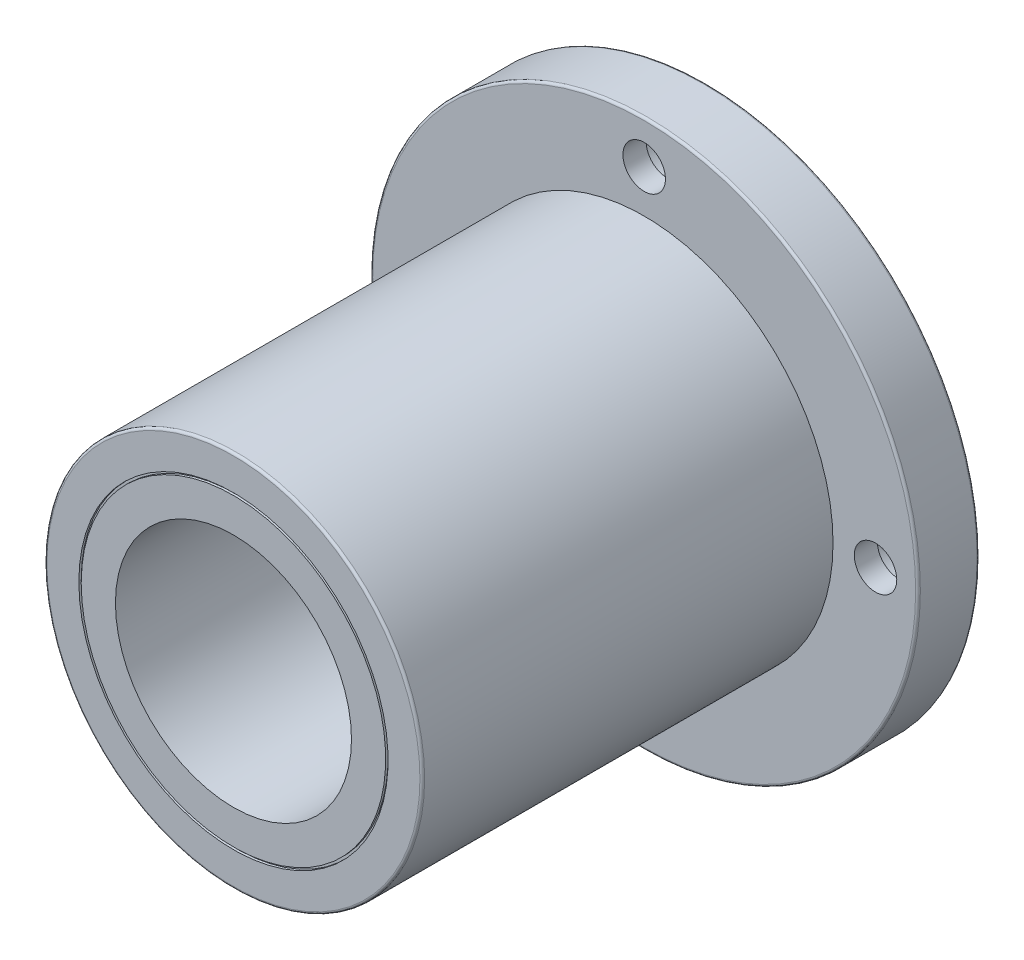
SolidWorks part; units mm, degrees
material "AISI 316 Отожженная нержавеющая сталь. полоса (SS)"
ref_plane "Plano frontal" through (0, 0, 0) normal (0, 0, 1) x (1, 0, 0)
ref_plane "Plano superior" through (0, 0, 0) normal (0, 1, 0) x (1, 0, 0)
ref_plane "Plano direito" through (0, 0, 0) normal (1, 0, 0) x (0, 0, -1)
sketch "Esboço1" plane through (0, 0, 0) normal (1, 0, 0) x (0, 0, -1)
  line L0 (0, 25) -> (0, 32.25)
  line L1 (0, 58) -> (-13, 58)
  line L2 (-13, 58) -> (-13, 40)
  line L3 (-13, 40) -> (-100, 40)
  line L4 (-100, 40) -> (-100, 32.75)
  line L5 (-100, 25) -> (0, 25)
  line L6 (0, 0) -> (-226.2321, 0) construction
  line L7 (-100, 32.75) -> (-99.5, 32.75)
  line L8 (-99.5, 32.75) -> (-99.5, 32.25)
  line L9 (-99.5, 32.25) -> (-100, 32.25)
  line L10 (0, 40) -> (-0.5, 40)
  line L11 (-0.5, 40) -> (-0.5, 39.5)
  line L12 (-0.5, 39.5) -> (0, 39.5)
  line L13 (0, 40) -> (0, 58)
  line L14 (-100, 32.25) -> (-100, 25)
  line L15 (0, 32.75) -> (-0.5, 32.75)
  line L16 (-0.5, 32.75) -> (-0.5, 32.25)
  line L17 (-0.5, 32.25) -> (0, 32.25)
  line L18 (0, 32.75) -> (0, 39.5)
  dimension "D1" = 100
  dimension "D2" = 80
  dimension "D3" = 50
  dimension "D4" = 116
  dimension "D5" = 13
  dimension "D6" = 0.5
  dimension "D7" = 0.5
  dimension "D8" = 0.5
  dimension "D9" = 0.5
  dimension "D10" = 0.5
  dimension "D11" = 0.5
revolve "Revolução1" add sketch "Esboço1" angle 360 about L6
sketch "Esboço5" plane through (0, 0, 0) normal (1, 0, 0) x (0, 0, -1)
  line L0 (0, 56) -> (-8.1, 56)
  line L1 (0, -58) -> (0, 58) construction
  line L2 (-8.1, 56) -> (-8.1, 53.5)
  line L3 (-8.1, 53.5) -> (-13, 53.5)
  line L4 (-13, 58) -> (-13, -58) construction
  line L5 (-13, 53.5) -> (-13, 49)
  line L6 (-13, 49) -> (0, 49)
  line L7 (0, 49) -> (0, 56)
  line L8 (0, 49) -> (2.2336, 49) construction
  line L9 (0, 0) -> (9.7959, 0) construction
  dimension "D1" = 14
  dimension "D2" = 9
  dimension "D3" = 8.1
  dimension "D4" = 98
revolve "Corte-Revolução1" cut sketch "Esboço5" angle 360 about L8
pattern_circular "PadrãoCircular1" count 4 over 360 about axis through (0, 0, 0) along (0, 0, 1) of "Corte-Revolução1"
fillet "Filete1" radius 0.5 3 edges at (-58, 0, 0) (-58, 0, 13) (-40, 0, 100)
